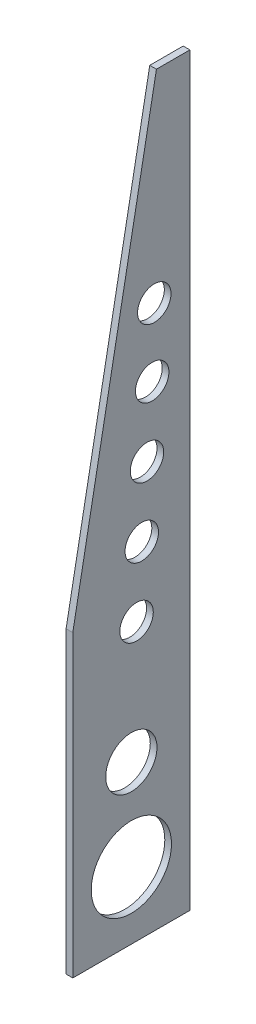
SolidWorks part; units mm, degrees
ref_plane "Front Plane" through (0, 0, 0) normal (0, 0, 1) x (1, 0, 0)
ref_plane "Top Plane" through (0, 0, 0) normal (0, 1, 0) x (1, 0, 0)
ref_plane "Right Plane" through (0, 0, 0) normal (1, 0, 0) x (0, 0, -1)
sketch "Sketch1" plane through (0, 0, 0) normal (1, 0, 0) x (0, 0, -1)
  line L0 (189.5945, 101.4168) -> (189.5945, 308.1093) construction
  line L1 (167.3695, 308.1093) -> (167.3695, 358.9093)
  line L2 (167.3695, 308.1093) -> (211.8195, 308.1093) construction
  line L3 (167.3695, 308.1093) -> (167.3695, 76.0168)
  line L4 (167.3695, 76.0168) -> (211.8195, 76.0168)
  line L5 (211.8195, 308.1093) -> (211.8195, 76.0168)
  line L6 (167.3695, 358.9093) -> (211.8195, 358.9093)
  line L7 (211.8195, 358.9093) -> (211.8195, 308.1093)
  line L8 (167.3695, 257.3093) -> (211.8195, 257.3093) construction
  line L9 (199.1195, 358.9093) -> (167.3695, 189.576)
  line L10 (211.8195, 116.6568) -> (167.3695, 116.6568) construction
  line L11 (167.3695, 101.4168) -> (211.8195, 101.4168) construction
  line L12 (205.4695, 358.9093) -> (189.5945, 155.7093) construction
  line L13 (211.8195, 155.7093) -> (167.3695, 155.7093) construction
  line L14 (199.1195, 308.1093) -> (197.5079, 257.0007) construction
  line L16 (199.1195, 358.9093) -> (199.1195, 308.1093) construction
  circle A0 centre (189.5945, 135.8656) radius 9.7234
  circle A1 centre (189.5945, 135.8656) radius 22.225 construction
  circle A2 centre (189.5945, 101.4168) radius 15.24
  circle A3 centre (191.5729, 181.0322) radius 6.35
  circle A4 centre (193.5512, 206.355) radius 6.35
  circle A5 centre (195.5296, 231.6779) radius 6.35
  circle A6 centre (197.5079, 257.0007) radius 6.35
  circle A7 centre (198.3085, 282.3881) radius 6.35
  point P18 (189.5945, 104.208)
  point P20 (189.5945, 101.4168)
  point P41 (199.1195, 333.5093)
  dimension "D1" = 19.4469
  dimension "D9" = 30.48
  dimension "D14" = 12.7
  dimension "D16" = 12.7
  dimension "D17" = 12.7
  dimension "D18" = 12.7
  dimension "D21" = 12.7
  dimension "D5" = 50.8
  dimension "D4" = 44.45
  dimension "D7" = 50.8
  dimension "D8" = 12.7
  dimension "D2" = 25.4
  dimension "D3" = 19.8438
  dimension "D6" = 19.2087
  dimension "D10" = 54.2925
  dimension "D11" = 34.4487
  dimension "D12" = 172.2438
  dimension "D13" = 6.35
  dimension "D15" = 25.4
  dimension "D19" = 25.4
  dimension "D20" = 25.4
  dimension "D23" = 25.4
extrude "Boss-Extrude1" add sketch "Sketch1" along normal blind 2.54 contours L6 L9 L3 L4 L5 L7 A0
sketch "Sketch2" plane through (0, 0, -211.8195) normal (0, 0, -1) x (-1, 0, 0)
  line L0 (-2.54, 358.9093) -> (-2.54, 76.0168) construction
  line L1 (0, 358.9093) -> (-2.54, 358.9093)
  line L2 (0, 358.9093) -> (0, 257.3093)
  line L3 (0, 257.3093) -> (-2.54, 257.3093)
  line L4 (-2.54, 358.9093) -> (-2.54, 257.3093)
  dimension "D1" = 101.6
split line "Split Line1"
equation "\"D12@Sketch1\"=5*\"D11@Sketch1\""
